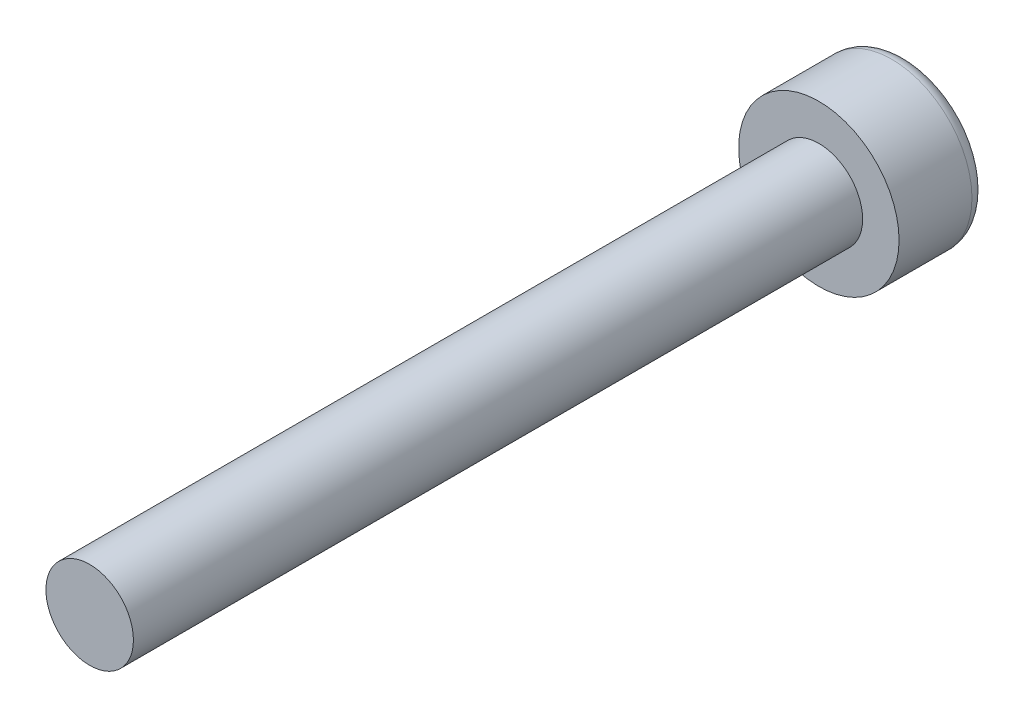
SolidWorks part; units mm, degrees
ref_plane "正面" through (0, 0, 0) normal (0, 0, 1) x (1, 0, 0)
ref_plane "平面" through (0, 0, 0) normal (0, 1, 0) x (1, 0, 0)
ref_plane "右側面" through (0, 0, 0) normal (1, 0, 0) x (0, 0, -1)
sketch "ｽｹｯﾁ2" plane through (0, 0, 0) normal (0, 0, 1) x (1, 0, 0)
  circle A0 centre (0, 0) radius 2.75
  dimension "D1" = 5.5
extrude "ﾎﾞｽ - 押し出し1" add sketch "ｽｹｯﾁ2" along normal blind 3
sketch "ｽｹｯﾁ3" plane through (0, 0, 3) normal (0, 0, 1) x (1, 0, 0)
  circle A0 centre (0, 0) radius 1.5
  dimension "D1" = 3
extrude "ﾎﾞｽ - 押し出し2" add sketch "ｽｹｯﾁ3" along normal blind 25
fillet "ﾌｨﾚｯﾄ1" radius 0.5 1 edges at (2.75, 0, 0)
